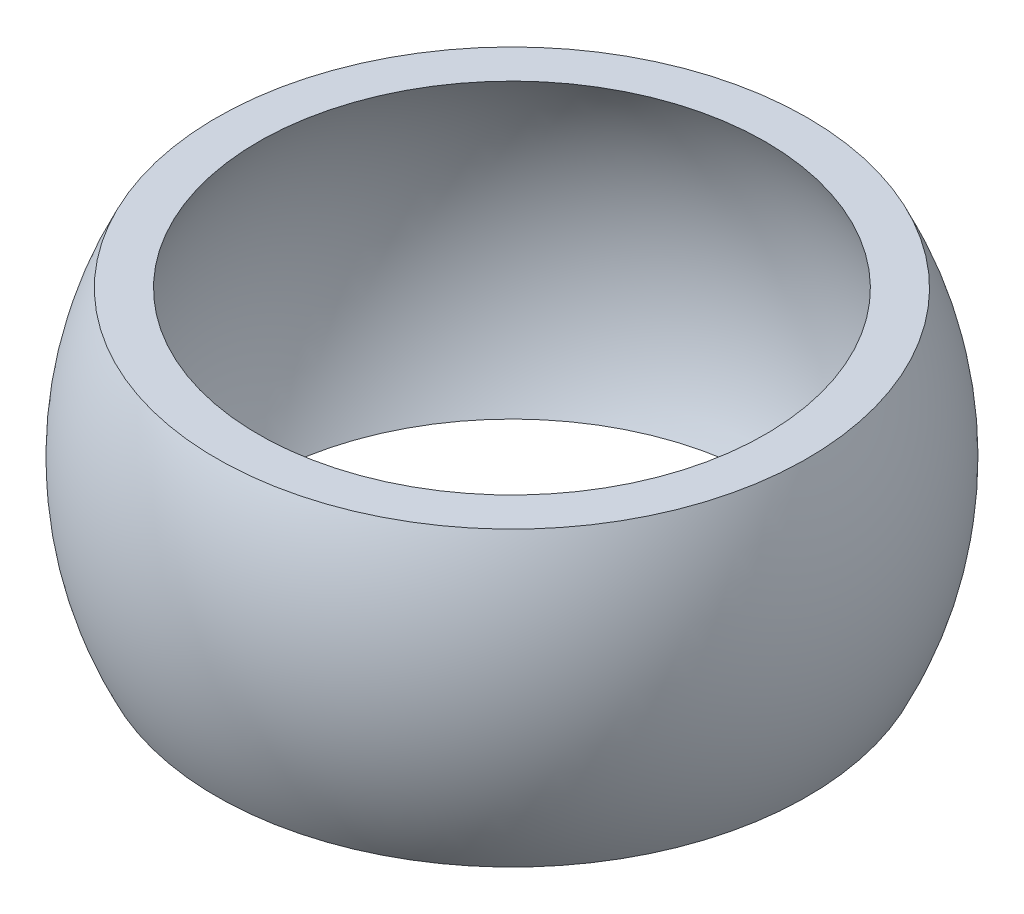
SolidWorks part; units mm, degrees
ref_plane "Front Plane" through (0, 0, 0) normal (0, 0, 1) x (1, 0, 0)
ref_plane "Top Plane" through (0, 0, 0) normal (0, 1, 0) x (1, 0, 0)
ref_plane "Right Plane" through (0, 0, 0) normal (1, 0, 0) x (0, 0, -1)
sketch "Sketch1" plane through (0, 0, 0) normal (0, 0, 1) x (1, 0, 0)
  line L0 (0, 0) -> (0, 28.2585) construction
  line L1 (0, 0) -> (14, 0) construction
  line L2 (12.1244, 7) -> (14.1244, 7)
  line L3 (12.1244, -7) -> (14.1244, -7)
  arc A0 (14, 0) -> (12.1244, 7) centre (0, 0) ccw
  arc A1 (14, 0) -> (12.1244, -7) centre (0, 0) cw
  arc A2 (14.1244, -7) -> (14.1244, 7) centre (0, 0) ccw
  dimension "D3" = 14
  dimension "D1" = 2
  dimension "D2" = 14
revolve "Revolve1" add sketch "Sketch1" angle 360 about L0
scale "Scale1" scale about centroid uniform scaling yes scale factor 0.25
